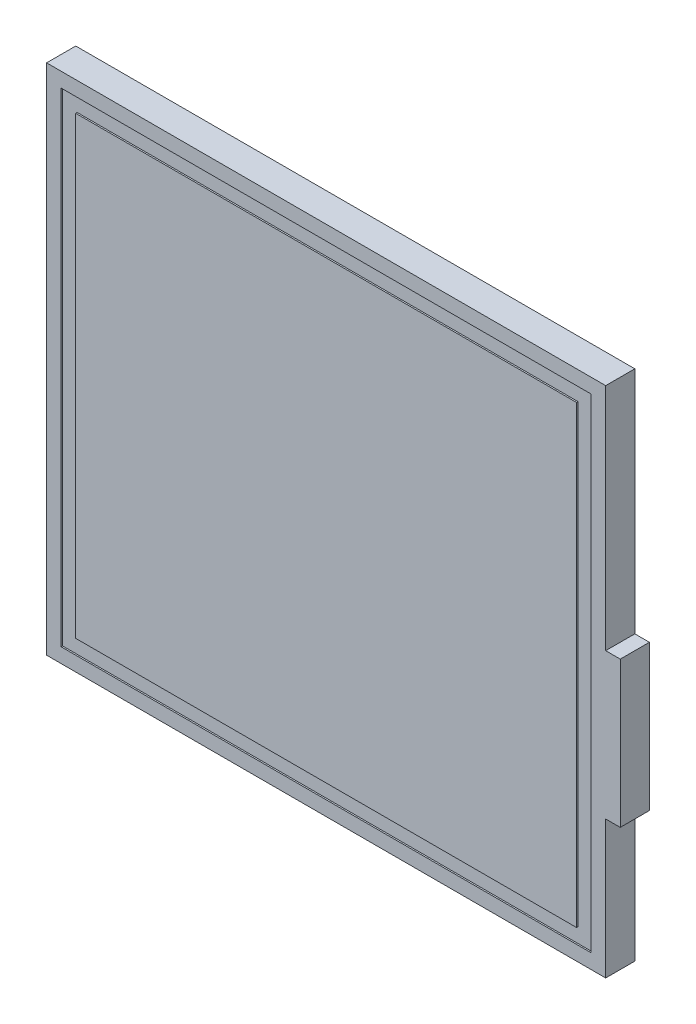
SolidWorks part; units mm, degrees
ref_plane "Front" through (0, 0, 0) normal (0, 0, 1) x (1, 0, 0)
ref_plane "Top" through (0, 0, 0) normal (0, 1, 0) x (1, 0, 0)
ref_plane "Right" through (0, 0, 0) normal (1, 0, 0) x (0, 0, -1)
sketch "COMPONENT_OUTLINE" plane through (0, 0, 0) normal (0, 0, 1) x (1, 0, 0)
  line L0 (19.18, -24.5) -> (20.18, -24.5)
  line L1 (20.18, -24.5) -> (20.18, -14.5)
  line L2 (20.18, -14.5) -> (19.18, -14.5)
  line L3 (19.18, -14.5) -> (19.18, 1.25)
  line L4 (19.18, 1.25) -> (-19.18, 1.25)
  line L5 (-19.18, 1.25) -> (-19.18, -33.95)
  line L6 (-19.18, -33.95) -> (19.18, -33.95)
  line L7 (19.18, -33.95) -> (19.18, -24.5)
extrude "Extrude1" add sketch "COMPONENT_OUTLINE" along normal blind 5
sketch "Sketch1" plane through (0, 0, 5) normal (0, 0, 1) x (1, 0, 0)
  line L8 (-17.18, -31.95) -> (17.18, -31.95)
  line L9 (17.18, -31.95) -> (17.18, -0.75)
  line L10 (17.18, -0.75) -> (-17.18, -0.75)
  line L11 (-17.18, -0.75) -> (-17.18, -31.95)
  line L16 (18.18, -32.95) -> (18.18, -23.5)
  line L17 (18.18, -23.5) -> (19.18, -23.5)
  line L18 (19.18, -23.5) -> (19.18, -15.5)
  line L19 (19.18, -15.5) -> (18.18, -15.5)
  line L20 (18.18, -15.5) -> (18.18, 0.25)
  line L21 (18.18, 0.25) -> (-18.18, 0.25)
  line L22 (-18.18, 0.25) -> (-18.18, -32.95)
  line L23 (-18.18, -32.95) -> (18.18, -32.95)
  line L28 (18.18, -32.95) -> (18.18, 0.25)
  line L29 (18.18, 0.25) -> (-18.18, 0.25)
  line L30 (-18.18, 0.25) -> (-18.18, -32.95)
  line L31 (-18.18, -32.95) -> (18.18, -32.95)
  dimension "D1" = 1
  dimension "D2" = 1
sketch "Sketch2" plane through (0, 0, 0) normal (0, 0, -1) x (-1, 0, 0)
  line L16 (-16.18, -21.5) -> (-16.18, -30.95)
  line L17 (-16.18, -30.95) -> (16.18, -30.95)
  line L18 (16.18, -30.95) -> (16.18, -1.75)
  line L19 (16.18, -1.75) -> (-16.18, -1.75)
  line L20 (-16.18, -1.75) -> (-16.18, -17.5)
  line L21 (-16.18, -17.5) -> (-17.18, -17.5)
  line L22 (-17.18, -17.5) -> (-17.18, -21.5)
  line L23 (-17.18, -21.5) -> (-16.18, -21.5)
  line L24 (-16.18, -21.5) -> (-16.18, -30.95)
  line L25 (-16.18, -30.95) -> (16.18, -30.95)
  line L26 (16.18, -30.95) -> (16.18, -1.75)
  line L27 (16.18, -1.75) -> (-16.18, -1.75)
  line L28 (-16.18, -1.75) -> (-16.18, -17.5)
  line L29 (-16.18, -17.5) -> (-17.18, -17.5)
  line L30 (-17.18, -17.5) -> (-17.18, -21.5)
  line L31 (-17.18, -21.5) -> (-16.18, -21.5)
  line L32 (-19.18, -24.5) -> (-19.18, -33.95)
  line L33 (-19.18, -33.95) -> (19.18, -33.95)
  line L34 (19.18, -33.95) -> (19.18, 1.25)
  line L35 (19.18, 1.25) -> (-19.18, 1.25)
  line L36 (-19.18, 1.25) -> (-19.18, -14.5)
  line L37 (-19.18, -14.5) -> (-20.18, -14.5)
  line L38 (-20.18, -14.5) -> (-20.18, -24.5)
  line L39 (-20.18, -24.5) -> (-19.18, -24.5)
  line L40 (-19.18, -24.5) -> (-19.18, -33.95)
  line L41 (-19.18, -33.95) -> (19.18, -33.95)
  line L42 (19.18, -33.95) -> (19.18, 1.25)
  line L43 (19.18, 1.25) -> (-19.18, 1.25)
  line L44 (-19.18, 1.25) -> (-19.18, -14.5)
  line L45 (-19.18, -14.5) -> (-20.18, -14.5)
  line L46 (-20.18, -14.5) -> (-20.18, -24.5)
  line L47 (-20.18, -24.5) -> (-19.18, -24.5)
  dimension "D1" = 3
  dimension "D2" = 0
extrude "Cut-Extrude1" cut sketch "Sketch2" against normal blind 3
extrude "Cut-Extrude2" cut sketch "Sketch1" against normal blind 0.1
